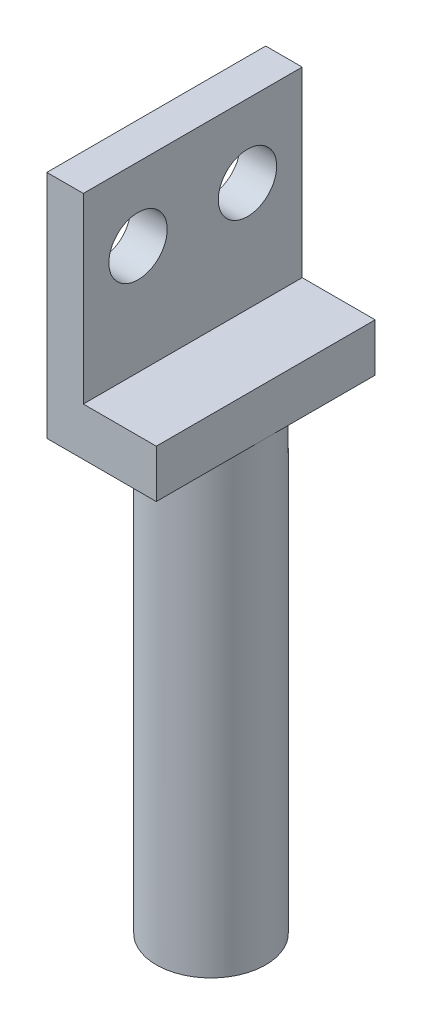
SolidWorks part; units mm, degrees
ref_plane "Front" through (0, 0, 0) normal (0, 0, 1) x (1, 0, 0)
ref_plane "Top" through (0, 0, 0) normal (0, 1, 0) x (1, 0, 0)
ref_plane "Right" through (0, 0, 0) normal (1, 0, 0) x (0, 0, -1)
sketch "草图1" plane through (0, 0, 0) normal (0, 1, 0) x (1, 0, 0)
  line L0 (0, 0) -> (8, 0) construction
  circle A0 centre (0, 0) radius 12.25
  circle A2 centre (8, 0) radius 1.25
  circle A3 centre (0, -8) radius 1.25
  circle A4 centre (-8, 0) radius 1.25
  circle A5 centre (0, 8) radius 1.25
  point P15 (0, 0)
  dimension "D1" = 4
extrude "凸台-拉伸1" add sketch "草图1" along normal blind 2
sketch "草图2" plane through (0, 2, 0) normal (0, 1, 0) x (1, 0, 0)
  circle A0 centre (0, 0) radius 3
extrude "凸台-拉伸2" add sketch "草图2" along normal blind 10.63
sketch "草图3" plane through (0, 12.63, 0) normal (0, 1, 0) x (1, 0, 0)
  line L0 (0, 0) -> (-1, 0) construction
  line L1 (-1, 0) -> (-1, 6) construction
  line L2 (-1, 6) -> (-3, 6) construction
  line L3 (-3, 6) -> (-3, 0) construction
  line L4 (-3, 0) -> (-3, -6) construction
  line L5 (-3, -6) -> (-1, -6) construction
  line L6 (-1, -6) -> (-1, 0) construction
  line L7 (-3, 6) -> (-1, 6)
  line L9 (-1, -6) -> (-3, -6)
  line L10 (-3, -6) -> (-3, 6)
  line L11 (-1, 6) -> (-1, -6)
  circle A0 centre (0, 0) radius 3 construction
  circle A1 centre (0, 0) radius 3 construction
extrude "凸台-拉伸3" add sketch "草图3" along normal blind 8
sketch "草图5" plane through (-1, 0, 0) normal (1, 0, 0) x (0, 0, -1)
  line L0 (0, 12.63) -> (0, 16.63) construction
  line L1 (-2.8284, 12.63) -> (2.8284, 12.63) construction
  line L2 (0, 16.63) -> (3, 16.63) construction
  circle A0 centre (3, 16.63) radius 1.6
  circle A1 centre (-3, 16.63) radius 1.6
extrude "切除-拉伸1" cut sketch "草图5" against normal blind 10
sketch "草图6" plane through (0, 2, 0) normal (0, 1, 0) x (1, 0, 0)
  line L0 (-3, 0) -> (-3, 6) construction
  line L1 (-3, 6) -> (-3, -6) construction
  line L2 (-1, 6) -> (-3, 6) construction
  line L3 (-3, 6) -> (3, 6) construction
  line L4 (3, 6) -> (3, 0) construction
  line L5 (-3, -6) -> (-3, 6)
  line L6 (-3, 6) -> (3, 6)
  line L7 (3, 6) -> (3, -6)
  line L8 (-3, 0) -> (0, 0) construction
  line L9 (-3, -6) -> (3, -6)
  arc A0 (-1, -2.8284) -> (-1, 2.8284) centre (0, 0) ccw construction
extrude "凸台-拉伸4" add sketch "草图6" along normal blind 10.63
sketch "草图7" plane through (0, 12.63, 0) normal (0, 1, 0) x (1, 0, 0)
  line L0 (-1, 6) -> (3, 6)
  line L1 (3, 6) -> (3, -6)
  line L2 (3, -6) -> (-1, -6)
  line L3 (-1, -6) -> (-1, 6)
extrude "切除-拉伸2" cut sketch "草图7" against normal blind 2
sketch "草图8" plane through (0, 0, 0) normal (0, -1, 0) x (1, 0, 0)
  circle A0 centre (0, 0) radius 12.25
extrude "切除-拉伸3" cut sketch "草图8" against normal blind 8
sketch "草图9" plane through (0, 8, 0) normal (0, -1, 0) x (1, 0, 0)
  circle A0 centre (0, 0) radius 3
extrude "凸台-拉伸5" add sketch "草图9" along normal blind 25
